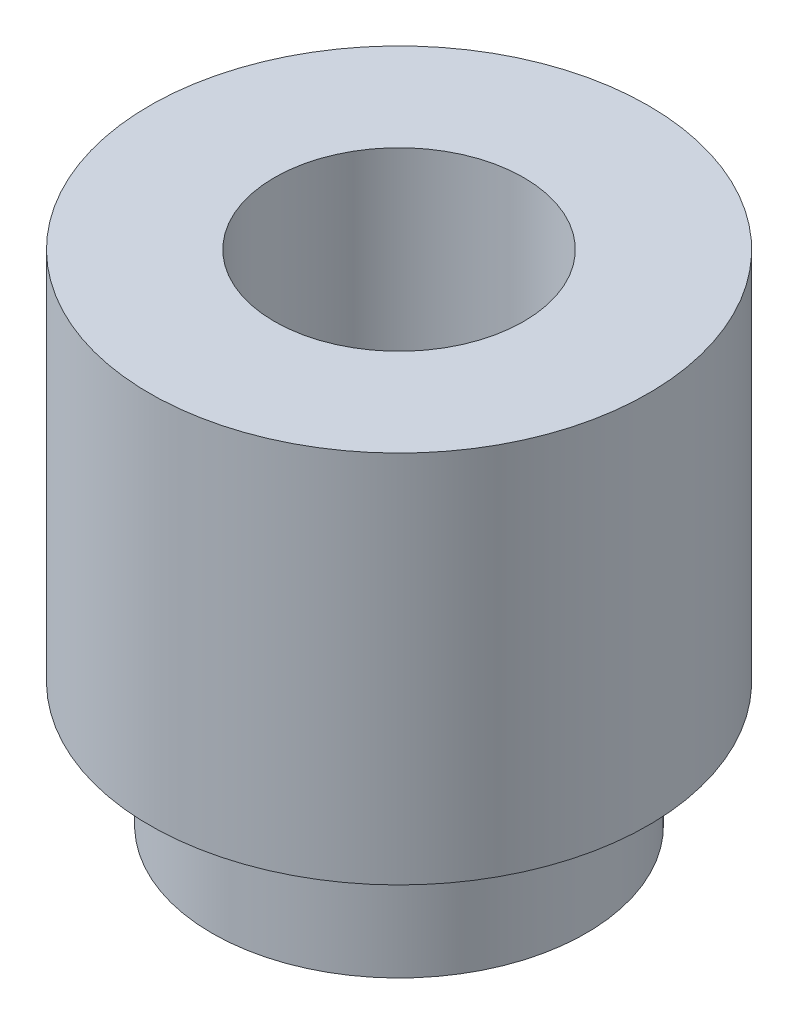
SolidWorks part; units mm, degrees
material "Brass"
ref_plane "Front Plane" through (0, 0, 0) normal (0, 0, 1) x (1, 0, 0)
ref_plane "Top Plane" through (0, 0, 0) normal (0, 1, 0) x (1, 0, 0)
ref_plane "Right Plane" through (0, 0, 0) normal (1, 0, 0) x (0, 0, -1)
sketch "Sketch1" plane through (0, 0, 0) normal (1, 0, 0) x (0, 0, -1)
  line L0 (0, 0) -> (0, 3.2899) construction
  line L1 (1, 4) -> (1, 0)
  line L2 (1, 0) -> (1.5, 0)
  line L3 (1.5, 0) -> (1.5, 1)
  line L4 (1.5, 1) -> (2, 1)
  line L5 (2, 1) -> (2, 4)
  line L6 (2, 4) -> (1, 4)
  dimension "D1" = 2
  dimension "D2" = 4
  dimension "D3" = 1
  dimension "D4" = 3
  dimension "D5" = 4
revolve "Revolve1" add sketch "Sketch1" angle 360 about L0
